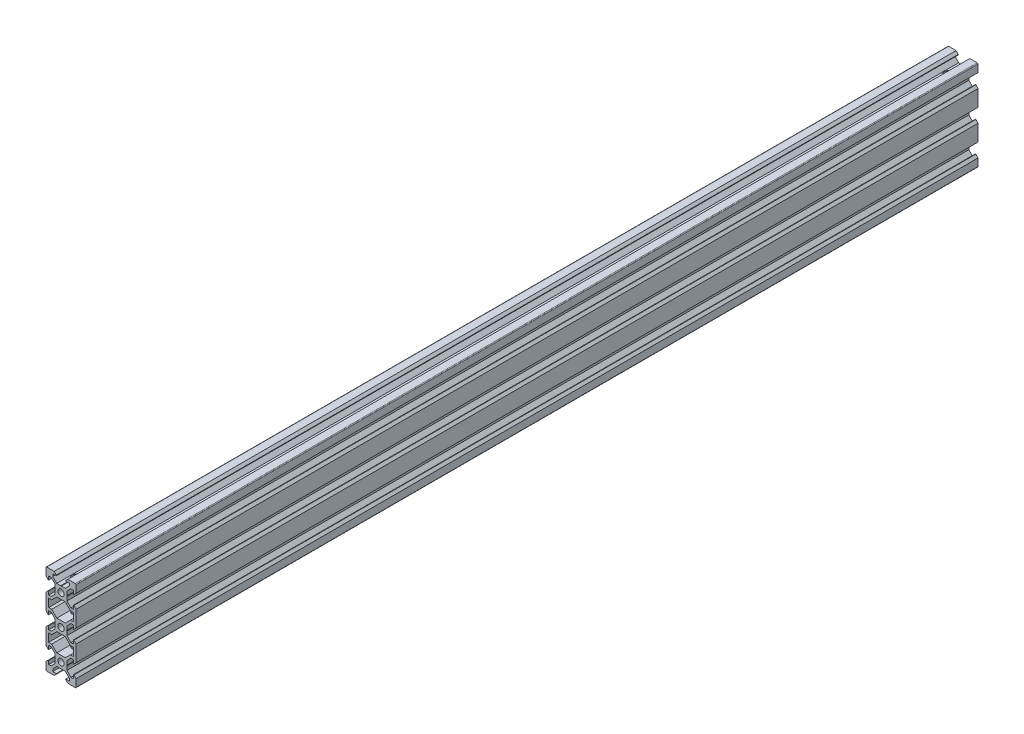
SolidWorks part; units mm, degrees
material "6061-T6 (SS)"
ref_plane "Front Plane" through (0, 0, 0) normal (0, 0, 1) x (1, 0, 0)
ref_plane "Top Plane" through (0, 0, 0) normal (0, 1, 0) x (1, 0, 0)
ref_plane "Right Plane" through (0, 0, 0) normal (1, 0, 0) x (0, 0, -1)
sketch "Sketch1" plane through (0, 0, 0) normal (0, 0, 1) x (1, 0, 0)
  line L0 (0, 0) -> (10, 0) construction
  line L1 (9.5, -30) -> (-9.5, -30)
  line L2 (10, -29.5) -> (10, 29.5)
  line L3 (9.5, 30) -> (-9.5, 30)
  line L4 (-10, -29.5) -> (-10, 29.5)
  line L5 (10, -30) -> (-10, 30) construction
  line L6 (10, 30) -> (-10, -30) construction
  circle A0 centre (0, 20) radius 2.1
  circle A1 centre (0, 0) radius 2.1
  circle A2 centre (0, -20) radius 2.1
  arc A3 (-9.5, -30) -> (-10, -29.5) centre (-9.5, -29.5) cw
  arc A4 (9.5, -30) -> (10, -29.5) centre (9.5, -29.5) ccw
  arc A5 (10, 29.5) -> (9.5, 30) centre (9.5, 29.5) ccw
  arc A6 (-9.5, 30) -> (-10, 29.5) centre (-9.5, 29.5) ccw
  point P0 (0, 0)
  line B0 (0, 20) -> (0, 30) construction
  line B1 (0, 23.69) -> (-0.21, 23.9)
  line B2 (-0.21, 23.9) -> (-2.8393, 23.9)
  line B3 (-2.8393, 23.9) -> (-5.5, 26.5607)
  line B4 (-5.5, 26.5607) -> (-5.5, 28.2)
  line B5 (-5.5, 28.2) -> (-3.125, 28.2)
  line B6 (-3.125, 28.2) -> (-3.125, 28.545)
  line B7 (-3.125, 28.545) -> (-4.58, 30)
  line B8 (-4.58, 30) -> (4.58, 30)
  line B9 (0, 20) -> (-5.9132, 25.9132) construction
  line B10 (3.125, 28.545) -> (4.58, 30)
  line B11 (3.125, 28.2) -> (3.125, 28.545)
  line B12 (5.5, 28.2) -> (3.125, 28.2)
  line B13 (5.5, 26.5607) -> (5.5, 28.2)
  line B14 (2.8393, 23.9) -> (5.5, 26.5607)
  line B15 (0.21, 23.9) -> (2.8393, 23.9)
  line B16 (0, 23.69) -> (0.21, 23.9)
  line B17 (0, 20) -> (-10, 20) construction
  line B18 (-3.69, 20) -> (-3.9, 19.79)
  line B19 (-3.9, 19.79) -> (-3.9, 17.1607)
  line B20 (-3.9, 17.1607) -> (-6.5607, 14.5)
  line B21 (-6.5607, 14.5) -> (-8.2, 14.5)
  line B22 (-8.2, 14.5) -> (-8.2, 16.875)
  line B23 (-8.2, 16.875) -> (-8.545, 16.875)
  line B24 (-8.545, 16.875) -> (-10, 15.42)
  line B25 (-10, 15.42) -> (-10, 24.58)
  line B26 (0, 20) -> (-5.9132, 14.0868) construction
  line B27 (-8.545, 23.125) -> (-10, 24.58)
  line B28 (-8.2, 23.125) -> (-8.545, 23.125)
  line B29 (-8.2, 25.5) -> (-8.2, 23.125)
  line B30 (-6.5607, 25.5) -> (-8.2, 25.5)
  line B31 (-3.9, 22.8393) -> (-6.5607, 25.5)
  line B32 (-3.9, 20.21) -> (-3.9, 22.8393)
  line B33 (-3.69, 20) -> (-3.9, 20.21)
  line B34 (0, 0) -> (-10, 0) construction
  line B35 (-3.69, 0) -> (-3.9, -0.21)
  line B36 (-3.9, -0.21) -> (-3.9, -2.8393)
  line B37 (-3.9, -2.8393) -> (-6.5607, -5.5)
  line B38 (-6.5607, -5.5) -> (-8.2, -5.5)
  line B39 (-8.2, -5.5) -> (-8.2, -3.125)
  line B40 (-8.2, -3.125) -> (-8.545, -3.125)
  line B41 (-8.545, -3.125) -> (-10, -4.58)
  line B42 (-10, -4.58) -> (-10, 4.58)
  line B43 (0, 0) -> (-5.9132, -5.9132) construction
  line B44 (-8.545, 3.125) -> (-10, 4.58)
  line B45 (-8.2, 3.125) -> (-8.545, 3.125)
  line B46 (-8.2, 5.5) -> (-8.2, 3.125)
  line B47 (-6.5607, 5.5) -> (-8.2, 5.5)
  line B48 (-3.9, 2.8393) -> (-6.5607, 5.5)
  line B49 (-3.9, 0.21) -> (-3.9, 2.8393)
  line B50 (-3.69, 0) -> (-3.9, 0.21)
  line B51 (0, -20) -> (-10, -20) construction
  line B52 (-3.69, -20) -> (-3.9, -20.21)
  line B53 (-3.9, -20.21) -> (-3.9, -22.8393)
  line B54 (-3.9, -22.8393) -> (-6.5607, -25.5)
  line B55 (-6.5607, -25.5) -> (-8.2, -25.5)
  line B56 (-8.2, -25.5) -> (-8.2, -23.125)
  line B57 (-8.2, -23.125) -> (-8.545, -23.125)
  line B58 (-8.545, -23.125) -> (-10, -24.58)
  line B59 (-10, -24.58) -> (-10, -15.42)
  line B60 (0, -20) -> (-5.9132, -25.9132) construction
  line B61 (-8.545, -16.875) -> (-10, -15.42)
  line B62 (-8.2, -16.875) -> (-8.545, -16.875)
  line B63 (-8.2, -14.5) -> (-8.2, -16.875)
  line B64 (-6.5607, -14.5) -> (-8.2, -14.5)
  line B65 (-3.9, -17.1607) -> (-6.5607, -14.5)
  line B66 (-3.9, -19.79) -> (-3.9, -17.1607)
  line B67 (-3.69, -20) -> (-3.9, -19.79)
  line B68 (0, -20) -> (0, -30) construction
  line B69 (0, -23.69) -> (0.21, -23.9)
  line B70 (0.21, -23.9) -> (2.8393, -23.9)
  line B71 (2.8393, -23.9) -> (5.5, -26.5607)
  line B72 (5.5, -26.5607) -> (5.5, -28.2)
  line B73 (5.5, -28.2) -> (3.125, -28.2)
  line B74 (3.125, -28.2) -> (3.125, -28.545)
  line B75 (3.125, -28.545) -> (4.58, -30)
  line B76 (4.58, -30) -> (-4.58, -30)
  line B77 (0, -20) -> (5.9132, -25.9132) construction
  line B78 (-3.125, -28.545) -> (-4.58, -30)
  line B79 (-3.125, -28.2) -> (-3.125, -28.545)
  line B80 (-5.5, -28.2) -> (-3.125, -28.2)
  line B81 (-5.5, -26.5607) -> (-5.5, -28.2)
  line B82 (-2.8393, -23.9) -> (-5.5, -26.5607)
  line B83 (-0.21, -23.9) -> (-2.8393, -23.9)
  line B84 (0, -23.69) -> (-0.21, -23.9)
  line B85 (0, -20) -> (10, -20) construction
  line B86 (3.69, -20) -> (3.9, -19.79)
  line B87 (3.9, -19.79) -> (3.9, -17.1607)
  line B88 (3.9, -17.1607) -> (6.5607, -14.5)
  line B89 (6.5607, -14.5) -> (8.2, -14.5)
  line B90 (8.2, -14.5) -> (8.2, -16.875)
  line B91 (8.2, -16.875) -> (8.545, -16.875)
  line B92 (8.545, -16.875) -> (10, -15.42)
  line B93 (10, -15.42) -> (10, -24.58)
  line B94 (0, -20) -> (5.9132, -14.0868) construction
  line B95 (8.545, -23.125) -> (10, -24.58)
  line B96 (8.2, -23.125) -> (8.545, -23.125)
  line B97 (8.2, -25.5) -> (8.2, -23.125)
  line B98 (6.5607, -25.5) -> (8.2, -25.5)
  line B99 (3.9, -22.8393) -> (6.5607, -25.5)
  line B100 (3.9, -20.21) -> (3.9, -22.8393)
  line B101 (3.69, -20) -> (3.9, -20.21)
  line B102 (0, 0) -> (10, 0) construction
  line B103 (3.69, 0) -> (3.9, 0.21)
  line B104 (3.9, 0.21) -> (3.9, 2.8393)
  line B105 (3.9, 2.8393) -> (6.5607, 5.5)
  line B106 (6.5607, 5.5) -> (8.2, 5.5)
  line B107 (8.2, 5.5) -> (8.2, 3.125)
  line B108 (8.2, 3.125) -> (8.545, 3.125)
  line B109 (8.545, 3.125) -> (10, 4.58)
  line B110 (10, 4.58) -> (10, -4.58)
  line B111 (0, 0) -> (5.9132, 5.9132) construction
  line B112 (8.545, -3.125) -> (10, -4.58)
  line B113 (8.2, -3.125) -> (8.545, -3.125)
  line B114 (8.2, -5.5) -> (8.2, -3.125)
  line B115 (6.5607, -5.5) -> (8.2, -5.5)
  line B116 (3.9, -2.8393) -> (6.5607, -5.5)
  line B117 (3.9, -0.21) -> (3.9, -2.8393)
  line B118 (3.69, 0) -> (3.9, -0.21)
  line B119 (0, 20) -> (10, 20) construction
  line B120 (3.69, 20) -> (3.9, 20.21)
  line B121 (3.9, 20.21) -> (3.9, 22.8393)
  line B122 (3.9, 22.8393) -> (6.5607, 25.5)
  line B123 (6.5607, 25.5) -> (8.2, 25.5)
  line B124 (8.2, 25.5) -> (8.2, 23.125)
  line B125 (8.2, 23.125) -> (8.545, 23.125)
  line B126 (8.545, 23.125) -> (10, 24.58)
  line B127 (10, 24.58) -> (10, 15.42)
  line B128 (0, 20) -> (5.9132, 25.9132) construction
  line B129 (8.545, 16.875) -> (10, 15.42)
  line B130 (8.2, 16.875) -> (8.545, 16.875)
  line B131 (8.2, 14.5) -> (8.2, 16.875)
  line B132 (6.5607, 14.5) -> (8.2, 14.5)
  line B133 (3.9, 17.1607) -> (6.5607, 14.5)
  line B134 (3.9, 19.79) -> (3.9, 17.1607)
  line B135 (3.69, 20) -> (3.9, 19.79)
  line B136 (-8.2, 7.3) -> (-8.2, 12.7)
  line B137 (-8.2, 12.7) -> (-6.2393, 12.7)
  line B138 (-6.2393, 12.7) -> (-2.8393, 16.1)
  line B139 (-2.8393, 16.1) -> (2.8393, 16.1)
  line B140 (0, 16.1) -> (0, 10) construction
  line B141 (0, 10) -> (-8.2, 10) construction
  line B142 (6.2393, 12.7) -> (2.8393, 16.1)
  line B143 (8.2, 12.7) -> (6.2393, 12.7)
  line B144 (8.2, 7.3) -> (8.2, 12.7)
  line B145 (8.2, 7.3) -> (6.2393, 7.3)
  line B146 (6.2393, 7.3) -> (2.8393, 3.9)
  line B147 (-2.8393, 3.9) -> (2.8393, 3.9)
  line B148 (-6.2393, 7.3) -> (-2.8393, 3.9)
  line B149 (-8.2, 7.3) -> (-6.2393, 7.3)
  line B150 (0, 16.1) -> (0, 20) construction
  line B151 (0, 20) -> (-5.0927, 14.9073) construction
  line B152 (-8.2, -12.7) -> (-8.2, -7.3)
  line B153 (-8.2, -7.3) -> (-6.2393, -7.3)
  line B154 (-6.2393, -7.3) -> (-2.8393, -3.9)
  line B155 (-2.8393, -3.9) -> (2.8393, -3.9)
  line B156 (0, -3.9) -> (0, -10) construction
  line B157 (0, -10) -> (-8.2, -10) construction
  line B158 (6.2393, -7.3) -> (2.8393, -3.9)
  line B159 (8.2, -7.3) -> (6.2393, -7.3)
  line B160 (8.2, -12.7) -> (8.2, -7.3)
  line B161 (8.2, -12.7) -> (6.2393, -12.7)
  line B162 (6.2393, -12.7) -> (2.8393, -16.1)
  line B163 (-2.8393, -16.1) -> (2.8393, -16.1)
  line B164 (-6.2393, -12.7) -> (-2.8393, -16.1)
  line B165 (-8.2, -12.7) -> (-6.2393, -12.7)
  line B166 (0, -3.9) -> (0, 0) construction
  line B167 (0, 0) -> (-5.0927, -5.0927) construction
  dimension "D3" = 4.2
  dimension "D5" = 0.5
  dimension "D1" = 20
  dimension "D2" = 60
  dimension "D4" = 40
sketch_block_instance "V Slot 1-4"
sketch_block "V Slot 1" parameters "D1"=10, "D2"=11, "D3"=4.3, "D4"=1.8, "D5"=0.21, "D6"=45, "D7"=9.16, "D8"=1.5, "D9"=6.25
sketch_block_instance "V Slot 1-5"
sketch_block_instance "V Slot 1-6"
sketch_block_instance "V Slot 1-7"
sketch_block_instance "V Slot 1-8"
sketch_block_instance "V Slot 1-9"
sketch_block_instance "V Slot 1-10"
sketch_block_instance "V Slot 1-11"
sketch_block_instance "Center Cutout 1-1"
sketch_block "Center Cutout 1" parameters "D1"=5.4, "D2"=12.2, "D3"=8.2, "D4"=45, "D5"=10, "D6"=1.5
sketch_block_instance "Center Cutout 1-2"
extrude "Boss-Extrude1" add sketch "Sketch1" along normal blind 600 contours B135 B120 B121 B122 B123 B124 B125 B126 L2 A5 L3 B10 B11 B12 B13 B14 B15 B16 B1 B2 B3 B4 B5 B6 B7 A6 L4 B27 B28 B29 B30 B31 B32 B33 B18 B19 B20 B21 B22 B23 B24 B44 B45 B46 B47 B48 B49 B50 B35
sketch "Sketch2" plane through (0, 0, 0) normal (0, 1, 0) x (1, 0, 0)
  line L0 (-10, -600) -> (-10, 0) construction
  line L1 (0.21, -600) -> (2.8393, -600) construction
  line L2 (-0.21, 0) -> (-2.8393, 0) construction
  circle A0 centre (0, -590) radius 2.55
  circle A1 centre (0, -10) radius 2.55
  dimension "D1" = 10
  dimension "D2" = 10
  dimension "D3" = 10
  dimension "D4" = 10
extrude "Cut-Extrude1" cut sketch "Sketch2" against normal through all both and the other way through all
